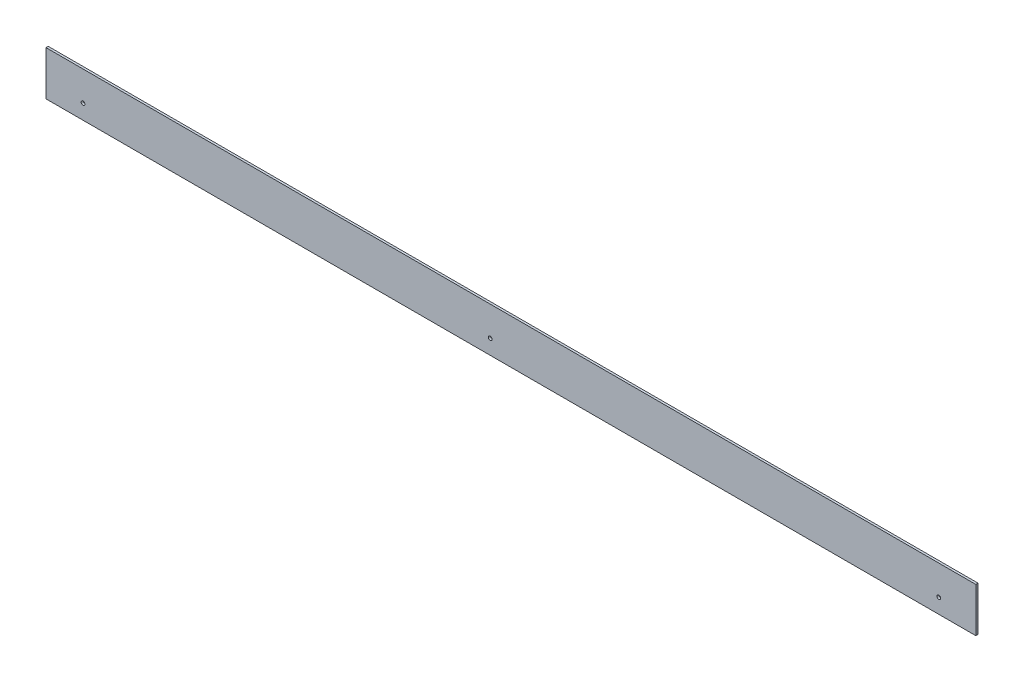
SolidWorks part; units mm, degrees
ref_plane "Front Plane" through (0, 0, 0) normal (0, 0, 1) x (1, 0, 0)
ref_plane "Top Plane" through (0, 0, 0) normal (0, 1, 0) x (1, 0, 0)
ref_plane "Right Plane" through (0, 0, 0) normal (1, 0, 0) x (0, 0, -1)
sketch "Sketch1" plane through (0, 0, 0) normal (0, 0, 1) x (1, 0, 0)
  line L1 (-628, 30) -> (628, 30)
  line L2 (-628, 30) -> (-628, -30)
  line L3 (-628, -30) -> (628, -30)
  line L4 (628, 30) -> (628, -30)
  line L5 (-628, 30) -> (628, -30) construction
  line L6 (-628, -30) -> (628, 30) construction
  circle A1 centre (-28, -10) radius 2.55
  circle A10 centre (578, -10) radius 2.55
  circle A11 centre (-578, -10) radius 2.55
  point P0 (0, 0)
  dimension "D3" = 40
  dimension "D8" = 50
  dimension "D9" = 40
  dimension "D10" = 50
  dimension "D11" = 5.1
  dimension "D1" = 60
  dimension "D2" = 1256
  dimension "D12" = 40
extrude "Boss-Extrude1" add sketch "Sketch1" along normal blind 3
